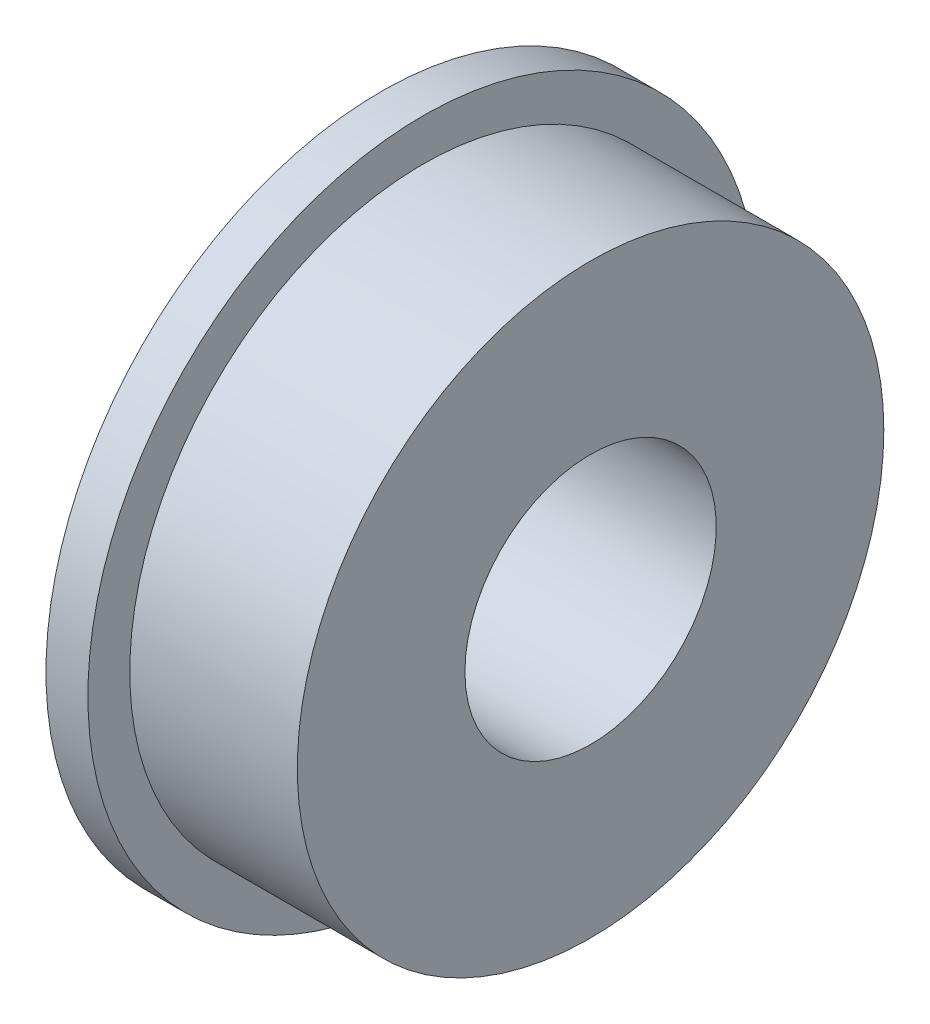
SolidWorks part; units mm, degrees
material "6061-T6 (SS)"
ref_plane "Front Plane" through (0, 0, 0) normal (0, 0, 1) x (1, 0, 0)
ref_plane "Top Plane" through (0, 0, 0) normal (0, 1, 0) x (1, 0, 0)
ref_plane "Right Plane" through (0, 0, 0) normal (1, 0, 0) x (0, 0, -1)
sketch "Sketch1" plane through (0, 0, 0) normal (1, 0, 0) x (0, 0, -1)
  circle A0 centre (0, 0) radius 25.4
  dimension "D1" = 50.8
extrude "Boss-Extrude1" add sketch "Sketch1" along normal blind 3.175
sketch "Sketch2" plane through (3.175, 0, 0) normal (1, 0, 0) x (0, 0, -1)
  circle A0 centre (0, 0) radius 22.225
  circle A1 centre (0, 0) radius 25.4 construction
  dimension "D1" = 3.175
extrude "Boss-Extrude2" add sketch "Sketch2" along normal blind 12.7
sketch "Sketch3" plane through (0, 0, 0) normal (-1, 0, 0) x (0, 0, 1)
  circle A0 centre (0, 0) radius 9.525
  dimension "D1" = 19.05
extrude "Cut-Extrude1" cut sketch "Sketch3" against normal through all
